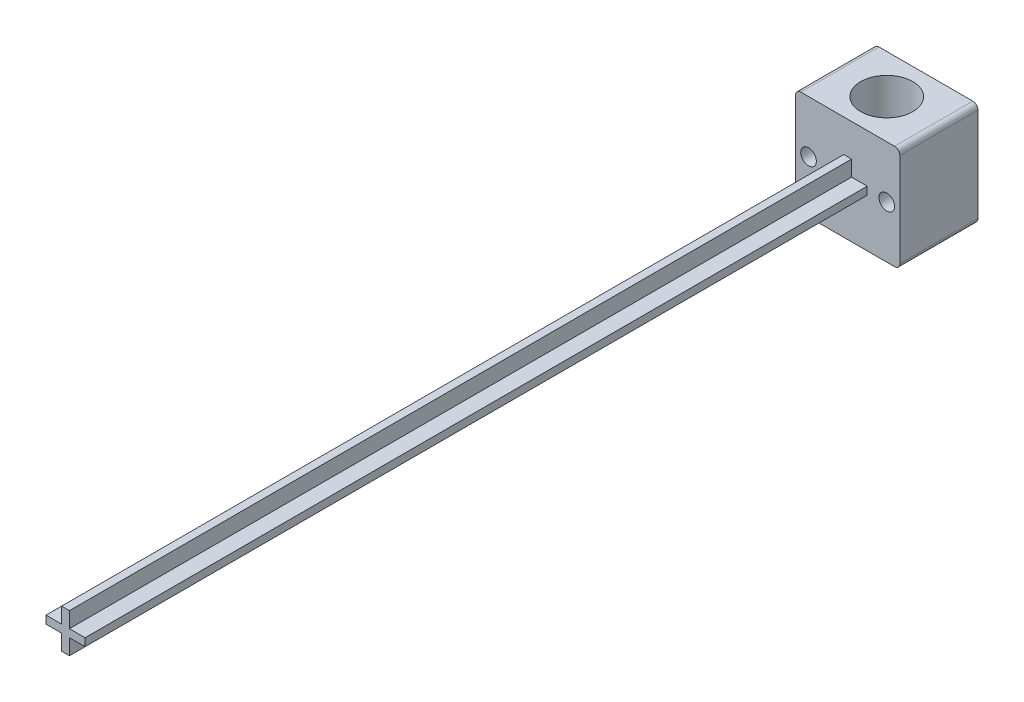
SolidWorks part; units mm, degrees
ref_plane "Front Plane" through (0, 0, 0) normal (0, 0, 1) x (1, 0, 0)
ref_plane "Top Plane" through (0, 0, 0) normal (0, 1, 0) x (1, 0, 0)
ref_plane "Right Plane" through (0, 0, 0) normal (1, 0, 0) x (0, 0, -1)
sketch "Sketch1" plane through (0, 0, 0) normal (0, 1, 0) x (1, 0, 0)
  line L1 (-10, 7.5) -> (10, 7.5)
  line L2 (-10, 7.5) -> (-10, -7.5)
  line L3 (-10, -7.5) -> (10, -7.5)
  line L4 (10, 7.5) -> (10, -7.5)
  line L5 (-10, 7.5) -> (10, -7.5) construction
  line L6 (-10, -7.5) -> (10, 7.5) construction
  circle A0 centre (0, 0) radius 5
  point P0 (0, 0)
  dimension "D3" = 10
  dimension "D1" = 20
  dimension "D2" = 15
extrude "Boss-Extrude1" add sketch "Sketch1" along normal blind 20
sketch "Sketch2" plane through (0, 0, 7.5) normal (0, 0, 1) x (1, 0, 0)
  circle A0 centre (7.5, 10) radius 1.5
  circle A1 centre (-7.5, 10) radius 1.5
  dimension "D2" = 3
extrude "Cut-Extrude2" cut sketch "Sketch2" against normal blind 20
sketch "Sketch4" plane through (0, 0, 7.5) normal (0, 0, 1) x (1, 0, 0)
  line L0 (0, 20) -> (0, 0) construction
  line L1 (-10, 20) -> (10, 20) construction
  line L2 (-10, 10) -> (10, 10) construction
  line L3 (-10, 20) -> (-10, 0) construction
  line L4 (10, 20) -> (10, 0) construction
  line L6 (-0.75, 13.75) -> (0.75, 13.75)
  line L7 (-0.75, 13.75) -> (-0.75, 6.25)
  line L8 (-0.75, 6.25) -> (0.75, 6.25)
  line L9 (0.75, 13.75) -> (0.75, 6.25)
  line L10 (-0.75, 13.75) -> (0.75, 6.25) construction
  line L11 (-0.75, 6.25) -> (0.75, 13.75) construction
  line L12 (-3.75, 10.75) -> (3.75, 10.75)
  line L13 (-3.75, 10.75) -> (-3.75, 9.25)
  line L14 (-3.75, 9.25) -> (3.75, 9.25)
  line L15 (3.75, 10.75) -> (3.75, 9.25)
  line L16 (-3.75, 10.75) -> (3.75, 9.25) construction
  line L17 (-3.75, 9.25) -> (3.75, 10.75) construction
  point P11 (0, 10)
  point P16 (0, 10)
  dimension "D1" = 1.5
  dimension "D2" = 7.5
  dimension "D3" = 7.5
  dimension "D4" = 1.5
extrude "Boss-Extrude3" add sketch "Sketch4" along normal blind 150 contours L12 L15 L14 L13 | L7 L8 L9 L6
fillet "Fillet3" radius 1 4 edges at (-10, 0, 0) (10, 0, 0) (10, 20, 0) (-10, 20, 0)
